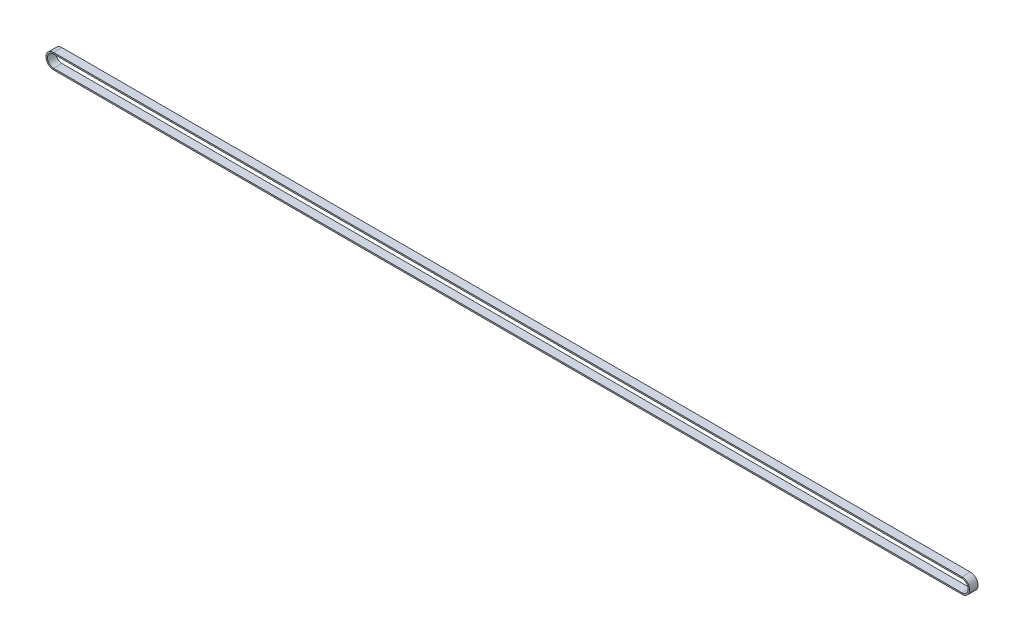
SolidWorks part; units mm, degrees
ref_plane "Front Plane" through (0, 0, 0) normal (0, 0, 1) x (1, 0, 0)
ref_plane "Top Plane" through (0, 0, 0) normal (0, 1, 0) x (1, 0, 0)
ref_plane "Right Plane" through (0, 0, 0) normal (1, 0, 0) x (0, 0, -1)
sketch "Sketch2" plane through (0, 0, 0) normal (0, 0, 1) x (1, 0, 0)
  line L0 (0, 0) -> (1, 0) construction
  line L1 (0, 0) -> (0, 1) construction
  line L2 (632.8676, -1418.5626) -> (-343.4633, -1418.5626)
  line L3 (-343.4633, -1402.2831) -> (632.8676, -1402.2831)
  arc A0 (632.8676, -1402.2831) -> (632.8676, -1418.5626) centre (632.8676, -1410.4229) cw
  arc A1 (-343.4633, -1418.5626) -> (-343.4633, -1402.2831) centre (-343.4633, -1410.4229) cw
ref_plane "Plane1" through (632.8676, -1402.2831, 0) normal (1, 0, 0) x (0, 0, -1)
sketch "Sketch3" plane through (632.8676, -1402.2831, 0) normal (1, 0, 0) x (0, 0, -1)
  line L1 (0, -1.5) -> (9, -1.5)
  line L2 (0, -1.5) -> (0, 0)
  line L3 (0, 0) -> (9, 0)
  line L4 (9, -1.5) -> (9, 0)
  dimension "D1" = 1.5
  dimension "D2" = 9
sweep "Sweep1" add profiles "Sketch3" path "Sketch2"
